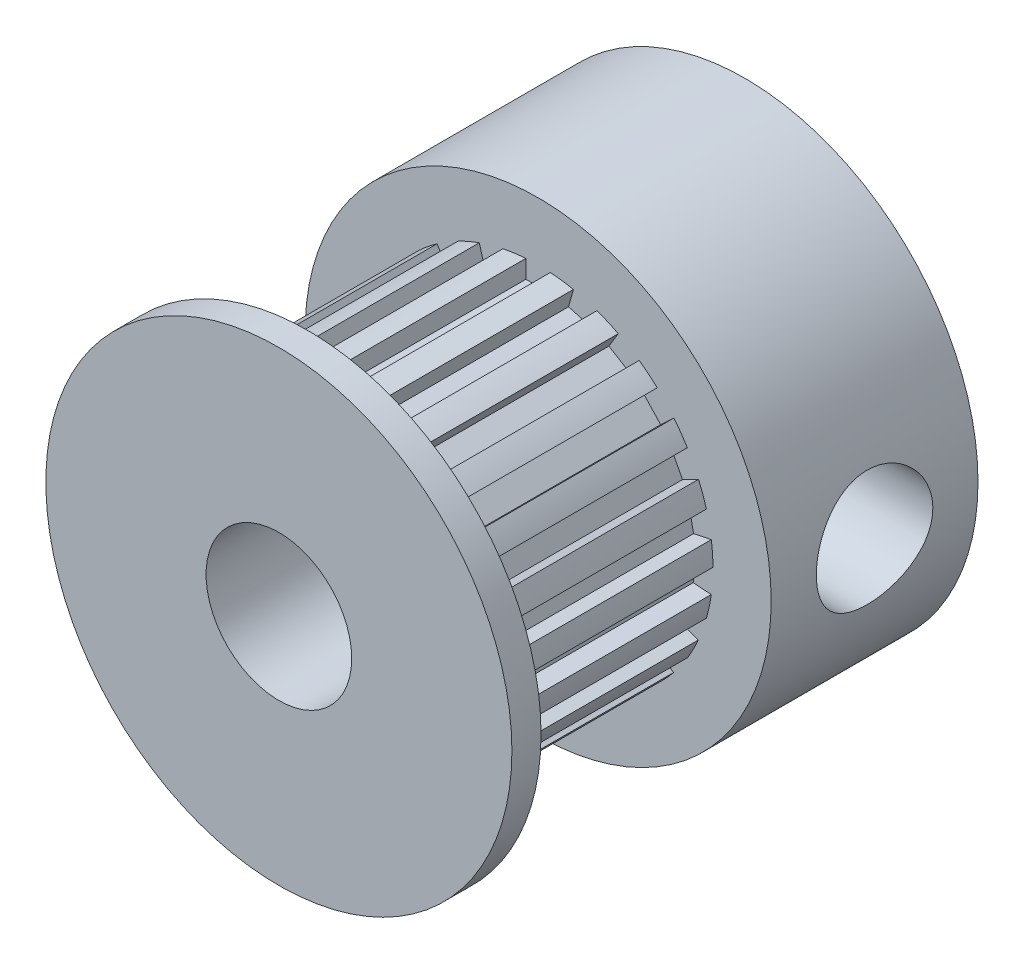
SolidWorks part; units mm, degrees
ref_plane "前视基准面" through (0, 0, 0) normal (0, 0, 1) x (1, 0, 0)
ref_plane "上视基准面" through (0, 0, 0) normal (0, 1, 0) x (1, 0, 0)
ref_plane "右视基准面" through (0, 0, 0) normal (1, 0, 0) x (0, 0, -1)
sketch "草图1" plane through (0, 0, 0) normal (0, 0, 1) x (1, 0, 0)
  circle A0 centre (0, 0) radius 8
  dimension "D1" = 16
extrude "凸台-拉伸1" add sketch "草图1" along normal blind 7.1
sketch "草图2" plane through (0, 0, 7.1) normal (0, 0, 1) x (1, 0, 0)
  circle A0 centre (0, 0) radius 6
  dimension "D1" = 12
extrude "凸台-拉伸2" add sketch "草图2" along normal blind 7.9
sketch "草图3" plane through (0, 0, 15) normal (0, 0, 1) x (1, 0, 0)
  circle A0 centre (0, 0) radius 8
  dimension "D1" = 16
extrude "凸台-拉伸3" add sketch "草图3" along normal blind 1
sketch "草图4" plane through (0, 0, 7.1) normal (0, 0, 1) x (1, 0, 0)
  line L0 (-6.0594, 0) -> (6.7938, 0) construction
  line L1 (0, 6.1) -> (0, -6.1) construction
  line L2 (1.3262, 6.2889) -> (1.0431, 5.2785)
  line L3 (-0.4197, 6.4135) -> (0.4197, 6.4135)
  line L4 (-0.4197, 6.4135) -> (-0.4197, 5.3642)
  line L5 (-0.4197, 5.3642) -> (0.4197, 5.3642)
  line L6 (0.4197, 6.4135) -> (0.4197, 5.3642)
  line L7 (-0.4197, 6.4135) -> (0.4197, 5.3642) construction
  line L8 (-0.4197, 5.3642) -> (0.4197, 6.4135) construction
  line L9 (1.3262, 6.2889) -> (2.1345, 6.0624)
  line L10 (2.1345, 6.0624) -> (1.8514, 5.0521)
  line L11 (1.0431, 5.2785) -> (1.8514, 5.0521)
  line L12 (2.9737, 5.6979) -> (2.4286, 4.8014)
  line L13 (2.9737, 5.6979) -> (3.6909, 5.2617)
  line L14 (3.6909, 5.2617) -> (3.1458, 4.3652)
  line L15 (2.4286, 4.8014) -> (3.1458, 4.3652)
  line L16 (4.4007, 4.6843) -> (3.6339, 3.9681)
  line L17 (4.4007, 4.6843) -> (4.9737, 4.0708)
  line L18 (4.9737, 4.0708) -> (4.2068, 3.3546)
  line L19 (3.6339, 3.9681) -> (4.2068, 3.3546)
  line L20 (5.5013, 3.3233) -> (4.5697, 2.8405)
  line L21 (5.5013, 3.3233) -> (5.8875, 2.578)
  line L22 (5.8875, 2.578) -> (4.9559, 2.0953)
  line L23 (4.5697, 2.8405) -> (4.9559, 2.0953)
  line L24 (6.1939, 1.7158) -> (5.1666, 1.5023)
  line L25 (6.1939, 1.7158) -> (6.3647, 0.8939)
  line L26 (6.3647, 0.8939) -> (5.3374, 0.6805)
  line L27 (5.1666, 1.5023) -> (5.3374, 0.6805)
  line L28 (6.4272, -0.019) -> (5.3804, 0.0526)
  line L29 (6.4272, -0.019) -> (6.3699, -0.8564)
  line L30 (6.3699, -0.8564) -> (5.3231, -0.7848)
  line L31 (5.3804, 0.0526) -> (5.3231, -0.7848)
  line L32 (6.1837, -1.7523) -> (5.1951, -1.4009)
  line L33 (6.1837, -1.7523) -> (5.9026, -2.5432)
  line L34 (5.9026, -2.5432) -> (4.914, -2.1918)
  line L35 (5.1951, -1.4009) -> (4.914, -2.1918)
  line L36 (5.4816, -3.3556) -> (4.6244, -2.7506)
  line L37 (5.4816, -3.3556) -> (4.9976, -4.0414)
  line L38 (4.9976, -4.0414) -> (4.1404, -3.4363)
  line L39 (4.6244, -2.7506) -> (4.1404, -3.4363)
  line L40 (4.373, -4.7101) -> (3.7109, -3.8962)
  line L41 (4.373, -4.7101) -> (3.7219, -5.2399)
  line L42 (3.7219, -5.2399) -> (3.0597, -4.426)
  line L43 (3.7109, -3.8962) -> (3.0597, -4.426)
  line L44 (2.9401, -5.7153) -> (2.5221, -4.7529)
  line L45 (2.9401, -5.7153) -> (2.1702, -6.0497)
  line L46 (2.1702, -6.0497) -> (1.7522, -5.0873)
  line L47 (2.5221, -4.7529) -> (1.7522, -5.0873)
  line L48 (1.2891, -6.2966) -> (1.1462, -5.2571)
  line L49 (1.2891, -6.2966) -> (0.4575, -6.4109)
  line L50 (0.4575, -6.4109) -> (0.3146, -5.3714)
  line L51 (1.1462, -5.2571) -> (0.3146, -5.3714)
  line L52 (-0.4575, -6.4109) -> (-0.3146, -5.3714)
  line L53 (-0.4575, -6.4109) -> (-1.2891, -6.2966)
  line L54 (-1.2891, -6.2966) -> (-1.1462, -5.2571)
  line L55 (-0.3146, -5.3714) -> (-1.1462, -5.2571)
  line L56 (-2.1702, -6.0497) -> (-1.7522, -5.0873)
  line L57 (-2.1702, -6.0497) -> (-2.9401, -5.7153)
  line L58 (-2.9401, -5.7153) -> (-2.5221, -4.7529)
  line L59 (-1.7522, -5.0873) -> (-2.5221, -4.7529)
  line L60 (-3.7219, -5.2399) -> (-3.0597, -4.426)
  line L61 (-3.7219, -5.2399) -> (-4.373, -4.7101)
  line L62 (-4.373, -4.7101) -> (-3.7109, -3.8962)
  line L63 (-3.0597, -4.426) -> (-3.7109, -3.8962)
  line L64 (-4.9976, -4.0414) -> (-4.1404, -3.4363)
  line L65 (-4.9976, -4.0414) -> (-5.4816, -3.3556)
  line L66 (-5.4816, -3.3556) -> (-4.6244, -2.7506)
  line L67 (-4.1404, -3.4363) -> (-4.6244, -2.7506)
  line L68 (-5.9026, -2.5432) -> (-4.914, -2.1918)
  line L69 (-5.9026, -2.5432) -> (-6.1837, -1.7523)
  line L70 (-6.1837, -1.7523) -> (-5.1951, -1.4009)
  line L71 (-4.914, -2.1918) -> (-5.1951, -1.4009)
  line L72 (-6.3699, -0.8564) -> (-5.3231, -0.7848)
  line L73 (-6.3699, -0.8564) -> (-6.4272, -0.019)
  line L74 (-6.4272, -0.019) -> (-5.3804, 0.0526)
  line L75 (-5.3231, -0.7848) -> (-5.3804, 0.0526)
  line L76 (-6.3647, 0.8939) -> (-5.3374, 0.6805)
  line L77 (-6.3647, 0.8939) -> (-6.1939, 1.7158)
  line L78 (-6.1939, 1.7158) -> (-5.1666, 1.5023)
  line L79 (-5.3374, 0.6805) -> (-5.1666, 1.5023)
  line L80 (-5.8875, 2.578) -> (-4.9559, 2.0953)
  line L81 (-5.8875, 2.578) -> (-5.5013, 3.3233)
  line L82 (-5.5013, 3.3233) -> (-4.5697, 2.8405)
  line L83 (-4.9559, 2.0953) -> (-4.5697, 2.8405)
  line L84 (-4.9737, 4.0708) -> (-4.2068, 3.3546)
  line L85 (-4.9737, 4.0708) -> (-4.4007, 4.6843)
  line L86 (-4.4007, 4.6843) -> (-3.6339, 3.9681)
  line L87 (-4.2068, 3.3546) -> (-3.6339, 3.9681)
  line L88 (-3.6909, 5.2617) -> (-3.1458, 4.3652)
  line L89 (-3.6909, 5.2617) -> (-2.9737, 5.6979)
  line L90 (-2.9737, 5.6979) -> (-2.4286, 4.8014)
  line L91 (-3.1458, 4.3652) -> (-2.4286, 4.8014)
  line L92 (-2.1345, 6.0624) -> (-1.8514, 5.0521)
  line L93 (-2.1345, 6.0624) -> (-1.3262, 6.2889)
  line L94 (-1.3262, 6.2889) -> (-1.0431, 5.2785)
  line L95 (-1.8514, 5.0521) -> (-1.0431, 5.2785)
  line L96 (0, 0) -> (0.4197, 5.3642) construction
  point P7 (0, 5.8889)
  dimension "D1" = 23
  dimension "D2" = 5.3806
extrude "切除-拉伸1" cut sketch "草图4" along normal up to surface (7.9 mm away) up to face at (8, 0, 15)
sketch "草图5" plane through (0, 0, 16) normal (0, 0, 1) x (1, 0, 0)
  circle A0 centre (0, 0) radius 2.5
  dimension "D1" = 5
extrude "切除-拉伸2" cut sketch "草图5" against normal blind 21
ref_plane "基准面1" through (8, 0, 0) normal (1, 0, 0) x (0, 0, -1)
sketch "草图6" plane through (8, 0, 0) normal (1, 0, 0) x (0, 0, -1)
  circle A0 centre (-3.55, 0) radius 2
  dimension "D1" = 4
extrude "切除-拉伸3" cut sketch "草图6" against normal up to surface (5.5 mm away) up to face at (2.5, 0, 16)
ref_plane "基准面2" through (0, -8, 0) normal (0, -1, 0) x (-1, 0, 0)
sketch "草图7" plane through (0, -8, 0) normal (0, -1, 0) x (-1, 0, 0)
  circle A0 centre (0, -3.55) radius 2
  dimension "D1" = 4
extrude "切除-拉伸4" cut sketch "草图7" against normal up to surface (5.5 mm away)
equation "\"7.1.00mm\"=0"
